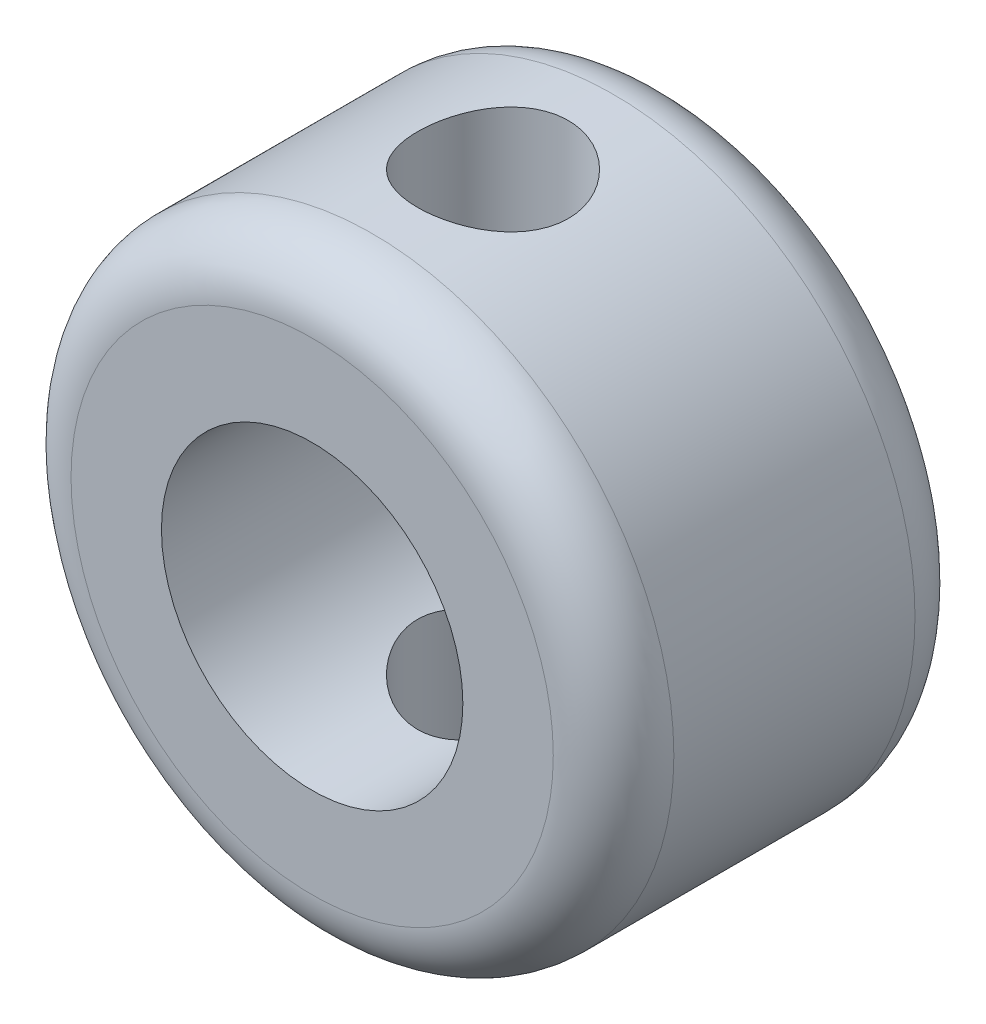
SolidWorks part; units mm, degrees
material "AISI 304"
ref_plane "Front Plane" through (0, 0, 0) normal (0, 0, 1) x (1, 0, 0)
ref_plane "Top Plane" through (0, 0, 0) normal (0, 1, 0) x (1, 0, 0)
ref_plane "Right Plane" through (0, 0, 0) normal (1, 0, 0) x (0, 0, -1)
sketch "Sketch1" plane through (0, 0, 0) normal (0, 0, 1) x (1, 0, 0)
  circle A0 centre (0, 0) radius 5
extrude "Boss-Extrude1" add sketch "Sketch1" along normal blind 6
fillet "Fillet3" radius 1 2 edges at (5, 0, 0) (5, 0, 6)
sketch "Sketch2" plane through (0, 0, 6) normal (0, 0, 1) x (1, 0, 0)
  circle A0 centre (0, 0) radius 2.5
extrude "Cut-Extrude1" cut sketch "Sketch2" against normal through all both and the other way through all
sketch "Sketch3" plane through (0, 0, 0) normal (0, 1, 0) x (1, 0, 0)
  circle A0 centre (0, -3) radius 1.25
  point P0 (0, -3)
extrude "Cut-Extrude2" cut sketch "Sketch3" against normal through all both and the other way through all
